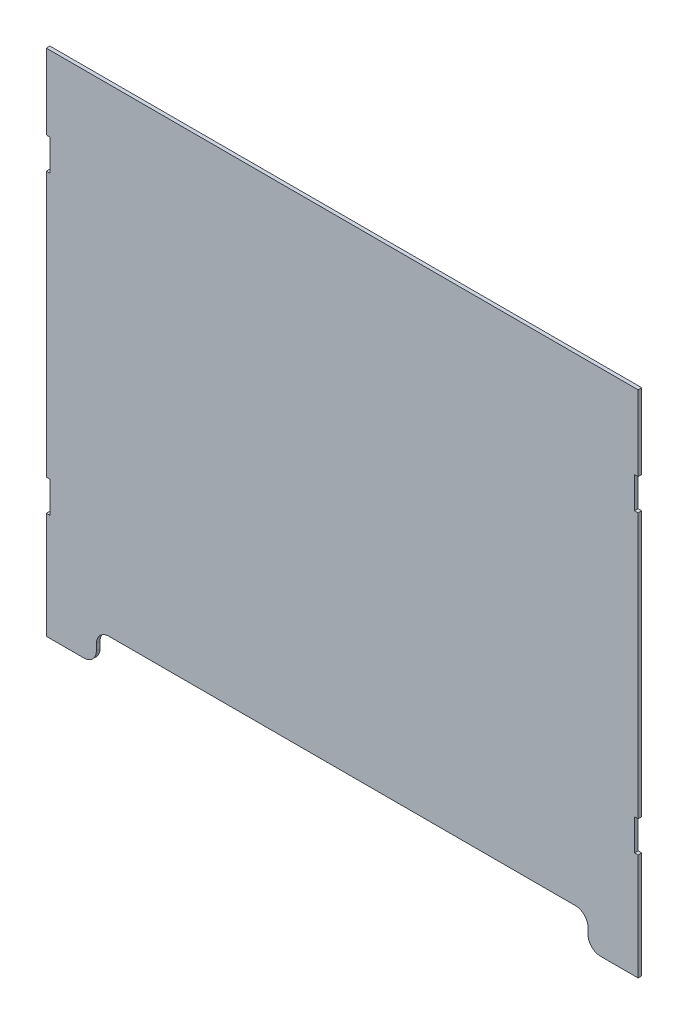
SolidWorks part; units mm, degrees
ref_plane "Front Plane" through (0, 0, 0) normal (0, 0, 1) x (1, 0, 0)
ref_plane "Top Plane" through (0, 0, 0) normal (0, 1, 0) x (1, 0, 0)
ref_plane "Right Plane" through (0, 0, 0) normal (1, 0, 0) x (0, 0, -1)
sketch "Sketch1" plane through (0, 0, 0) normal (0, 0, 1) x (1, 0, 0)
  line L0 (206.1, -203.2) -> (236.1, -203.2)
  line L1 (-236.1, -203.2) -> (-206.1, -203.2)
  line L2 (-236.1, -203.2) -> (-236.1, -118.2)
  line L3 (-236.1, 203.2) -> (236.1, 203.2)
  line L4 (236.1, -203.2) -> (236.1, -118.2)
  line L5 (-236.1, -203.2) -> (236.1, 203.2) construction
  line L6 (-236.1, 203.2) -> (236.1, -203.2) construction
  line L7 (236.1, 143.2) -> (236.1, 203.2)
  line L8 (-196.1, -193.2) -> (-196.1, -188.2)
  line L9 (-186.1, -178.2) -> (186.1, -178.2)
  line L10 (196.1, -193.2) -> (196.1, -188.2)
  line L11 (236.1, 143.2) -> (233.2, 143.2)
  line L12 (236.1, -93.2) -> (236.1, 118.2)
  line L13 (236.1, 118.2) -> (233.2, 118.2)
  line L14 (233.2, 143.2) -> (233.2, 118.2)
  line L15 (236.1, -93.2) -> (233.2, -93.2)
  line L16 (0, 203.2) -> (0, -178.2) construction
  line L17 (236.1, -118.2) -> (233.2, -118.2)
  line L18 (233.2, -93.2) -> (233.2, -118.2)
  line L19 (-236.1, -93.2) -> (-233.2, -93.2)
  line L20 (-233.2, -93.2) -> (-233.2, -118.2)
  line L21 (-236.1, -118.2) -> (-233.2, -118.2)
  line L22 (-236.1, 143.2) -> (-233.2, 143.2)
  line L23 (-233.2, 143.2) -> (-233.2, 118.2)
  line L24 (-236.1, 118.2) -> (-233.2, 118.2)
  line L25 (-236.1, 143.2) -> (-236.1, 203.2)
  line L26 (-236.1, -93.2) -> (-236.1, 118.2)
  arc A0 (-196.1, -188.2) -> (-186.1, -178.2) centre (-186.1, -188.2) cw
  arc A1 (-206.1, -203.2) -> (-196.1, -193.2) centre (-206.1, -193.2) ccw
  arc A2 (206.1, -203.2) -> (196.1, -193.2) centre (206.1, -193.2) cw
  arc A3 (186.1, -178.2) -> (196.1, -188.2) centre (186.1, -188.2) cw
  point P0 (0, 0)
  dimension "D6" = 10
  dimension "D1" = 406.4
  dimension "D2" = 472.2
  dimension "D3" = 25
  dimension "D4" = 40
  dimension "D5" = 40
  dimension "D7" = 2.9
  dimension "D8" = 60
  dimension "D9" = 25
  dimension "D10" = 25
  dimension "D11" = 2.9
  dimension "D12" = 85
extrude "Boss-Extrude1" add sketch "Sketch1" along normal blind 2.9
